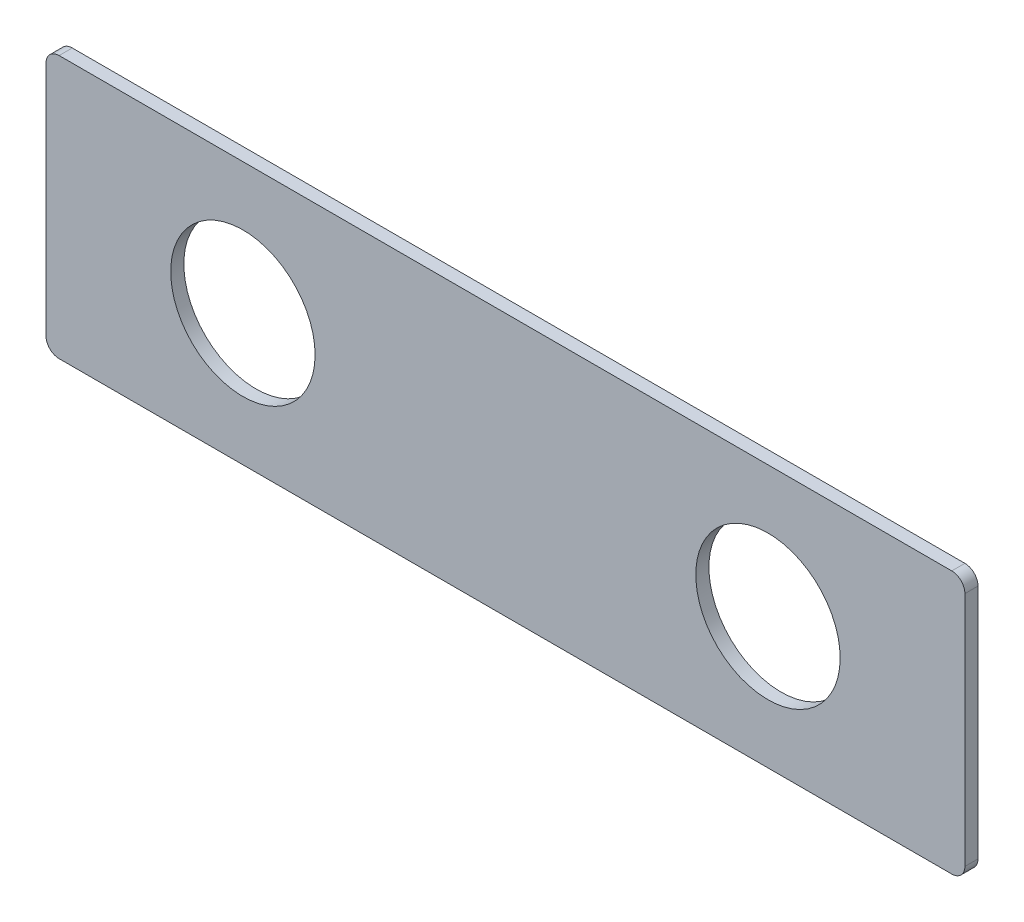
SolidWorks part; units mm, degrees
ref_plane "Plane1" through (0, 0, 0) normal (0, 0, 1) x (1, 0, 0)
ref_plane "Plane2" through (0, 0, 0) normal (0, 1, 0) x (1, 0, 0)
ref_plane "Plane3" through (0, 0, 0) normal (1, 0, 0) x (0, 0, -1)
sketch "Sketch3" plane through (0, 0, 0) normal (0, 0, 1) x (1, 0, 0)
  line L1 (34, 0) -> (-34, 0)
  line L2 (35, 1) -> (35, 19)
  line L3 (34, 20) -> (-34, 20)
  line L4 (-35, 1) -> (-35, 19)
  circle A0 centre (-20, 10) radius 5.5
  circle A1 centre (20, 10) radius 5.5
  arc A2 (-34, 0) -> (-35, 1) centre (-34, 1) cw
  arc A3 (-34, 20) -> (-35, 19) centre (-34, 19) ccw
  arc A4 (35, 19) -> (34, 20) centre (34, 19) ccw
  arc A5 (34, 0) -> (35, 1) centre (34, 1) ccw
  point P10 (-35, 0)
  point P13 (-35, 20)
  point P18 (35, 0)
  dimension "D4" = 40
  dimension "D6" = 11
  dimension "D7" = 1
  dimension "D1" = 70
  dimension "D2" = 20
  dimension "D3" = 15
  dimension "D5" = 10
extrude "Extrude2" add sketch "Sketch3" along normal mid plane 1
